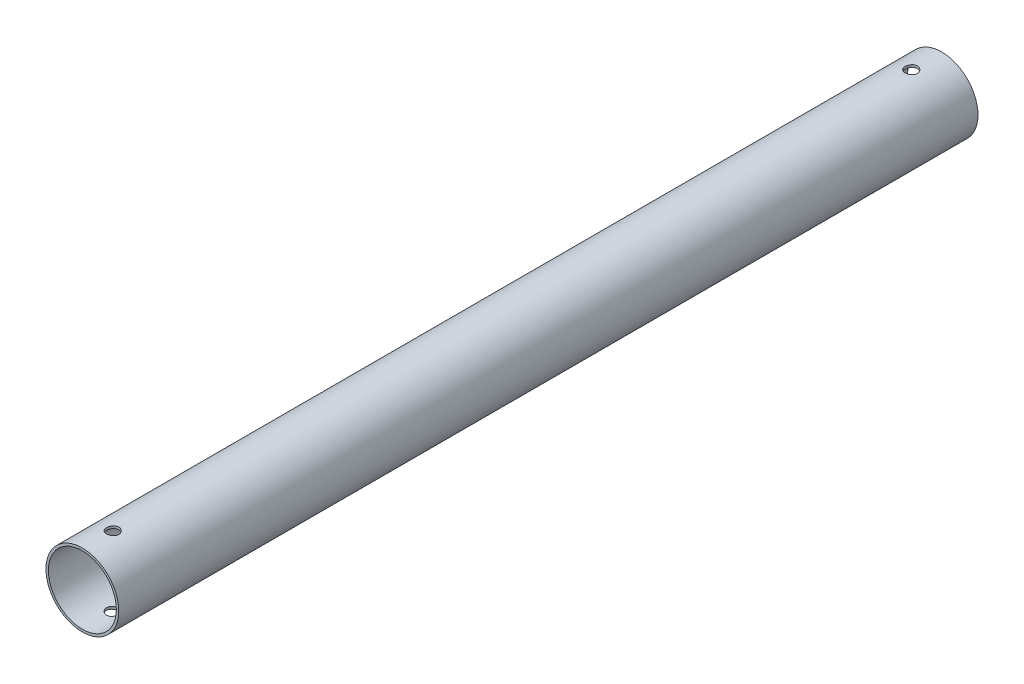
SolidWorks part; units mm, degrees
ref_plane "Front Plane" through (0, 0, 0) normal (0, 0, 1) x (1, 0, 0)
ref_plane "Top Plane" through (0, 0, 0) normal (0, 1, 0) x (1, 0, 0)
ref_plane "Right Plane" through (0, 0, 0) normal (1, 0, 0) x (0, 0, -1)
sketch "Sketch1" plane through (0, 0, 0) normal (0, 0, 1) x (1, 0, 0)
  circle A0 centre (0, 0) radius 30
  circle A1 centre (0, 0) radius 28
  dimension "D1" = 60
  dimension "D2" = 2
extrude "Boss-Extrude1" add sketch "Sketch1" along normal blind 708
sketch "Sketch2" plane through (0, 0, 0) normal (0, 1, 0) x (1, 0, 0)
  line L0 (-30, -708) -> (30, -708) construction
  line L1 (30, 0) -> (-30, 0) construction
  circle A0 centre (0, -683) radius 5
  circle A1 centre (0, -25) radius 5
  dimension "D2" = 10
  dimension "D3" = 10
  dimension "D1" = 25
  dimension "D4" = 25
extrude "Cut-Extrude1" cut sketch "Sketch2" against normal through all both and the other way through all
